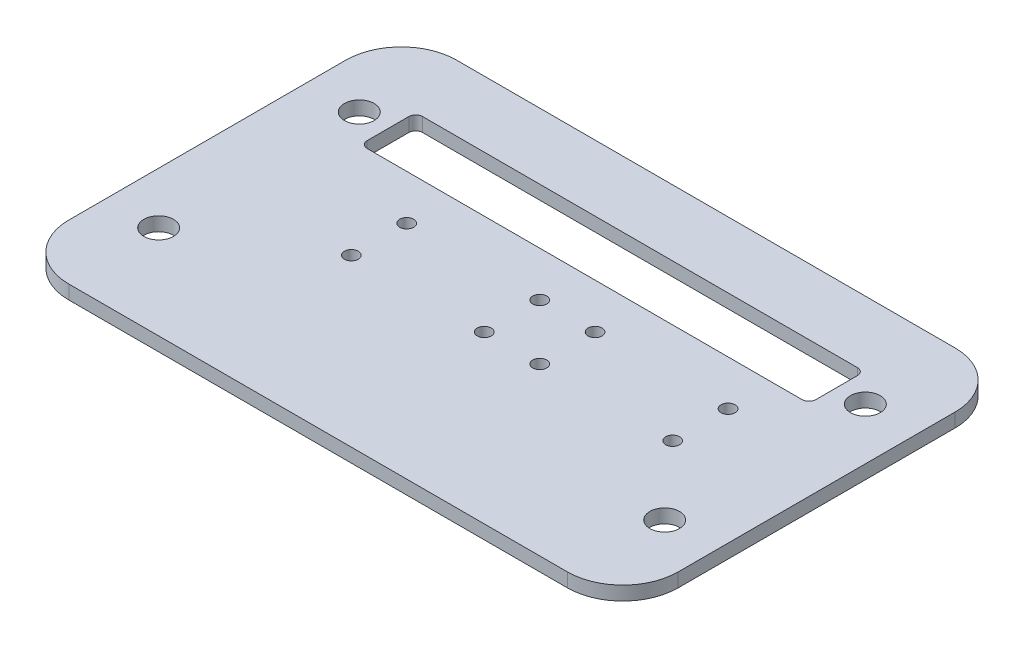
SolidWorks part; units mm, degrees
material "ABS"
ref_plane "Front Plane" through (0, 0, 0) normal (0, 0, 1) x (1, 0, 0)
ref_plane "Top Plane" through (0, 0, 0) normal (0, 1, 0) x (1, 0, 0)
ref_plane "Right Plane" through (0, 0, 0) normal (1, 0, 0) x (0, 0, -1)
sketch "Sketch2" plane through (0, 0, 0) normal (0, 1, 0) x (1, 0, 0)
  line L1 (-29, -11.5) -> (29, -11.5) construction
  line L2 (-29, -11.5) -> (-29, 11.5) construction
  line L3 (-29, 11.5) -> (29, 11.5) construction
  line L4 (29, -11.5) -> (29, 11.5) construction
  line L5 (-29, -11.5) -> (29, 11.5) construction
  line L6 (-29, 11.5) -> (29, -11.5) construction
  point P0 (0, 0)
  dimension "D1" = 58
  dimension "D2" = 23
sketch "Sketch3" plane through (0, 0, 0) normal (0, 1, 0) x (1, 0, 0)
  line L1 (-34.925, -22.225) -> (34.925, -22.225)
  line L2 (-34.925, -22.225) -> (-34.925, 22.225)
  line L3 (-34.925, 22.225) -> (34.925, 22.225)
  line L4 (34.925, -22.225) -> (34.925, 22.225)
  line L5 (-34.925, -22.225) -> (34.925, 22.225) construction
  line L6 (-34.925, 22.225) -> (34.925, -22.225) construction
  point P0 (0, 0)
  dimension "D1" = 44.45
  dimension "D2" = 69.85
extrude "Boss-Extrude1" add sketch "Sketch3" along normal blind 1.5875
hole_wizard "M3 Clearance Hole1" positions "Sketch4" profile "Sketch5" hole size "M3" standard "ANSI Metric" end condition through all
sketch "Sketch4" plane through (0, 1.5875, 0) normal (0, 1, 0) x (1, 0, 0)
  point P0 (-29, 11.5)
  point P3 (-29, -11.5)
  point P6 (29, -11.5)
  point P9 (29, 11.5)
sketch "Sketch5" plane through (-29, 1.5875, -11.5) normal (1, 0, 0) x (0, 0, 1)
  line L0 (0, 0) -> (0, 1.5875)
  line L1 (0, 1.5875) -> (1.7, 1.5875)
  line L2 (1.7, 1.5875) -> (1.7, 0)
  line L5 (1.7, 0) -> (0, 0)
  line L11 (0, -6.35) -> (0, 107.95) construction
  dimension "Thru Hole Dia." = 3.4
  dimension "Thru Hole Depth" = 1.5875
hole_wizard "Tap Drill for M2x0.4 Tap1" positions "Sketch6" profile "Sketch7" hole size "M2x0.4" standard "ANSI Metric" end condition through all
sketch "Sketch6" plane through (0, 1.5875, 0) normal (0, 1, 0) x (1, 0, 0)
  line L14 (0, 0) -> (34.925, 0) construction
  line L15 (34.925, -22.225) -> (34.925, 22.225) construction
  line L17 (-15.24, 3.175) -> (0, 3.175) construction
  line L20 (6.35, 3.175) -> (21.59, 3.175) construction
  line L23 (-15.24, -3.175) -> (0, -3.175) construction
  line L24 (0, 3.175) -> (0, -3.175) construction
  line L25 (6.35, -3.175) -> (21.59, -3.175) construction
  point P145 (-15.24, 3.175)
  point P148 (0, 3.175)
  point P151 (-15.24, -3.175)
  point P154 (0, -3.175)
  point P157 (6.35, 3.175)
  point P160 (21.59, 3.175)
  point P166 (0, 0)
  point P184 (6.35, -3.175)
  point P187 (21.59, -3.175)
  dimension "D1" = 15.24
  dimension "D2" = 6.35
  dimension "D3" = 6.35
  dimension "D4" = 6.35
sketch "Sketch7" plane through (21.59, 1.5875, 3.175) normal (1, 0, 0) x (0, 0, 1)
  line L0 (0, 0) -> (0, 1.5875)
  line L1 (0, 1.5875) -> (0.8, 1.5875)
  line L2 (0.8, 1.5875) -> (0.8, 0)
  line L5 (0.8, 0) -> (0, 0)
  line L11 (0, -6.35) -> (0, 107.95) construction
  dimension "Thru Hole Dia." = 1.6
  dimension "Thru Hole Depth" = 1.5875
fillet "Fillet1" radius 6.35 4 edges at (34.925, 0.7937, 22.225) (-34.925, 0.7937, -22.225) (34.925, 0.7937, -22.225) (-34.925, 0.7937, 22.225)
sketch "Sketch8" plane through (0, 1.5875, 0) normal (0, 1, 0) x (1, 0, 0)
  line L3 (-25.7125, 14.675) -> (25.7125, 14.675)
  line L7 (-25.7125, 14.675) -> (-25.7125, 8.325)
  line L8 (-25.7125, 8.325) -> (25.7125, 8.325)
  line L9 (25.7125, 14.675) -> (25.7125, 8.325)
  line L10 (-25.7125, 14.675) -> (25.7125, 8.325) construction
  line L11 (-25.7125, 8.325) -> (25.7125, 14.675) construction
  line L12 (-29, 11.5) -> (29, 11.5) construction
  circle A3 centre (-29, 11.5) radius 1.7 construction
  point P4 (0, 11.5)
  point P5 (0, 0)
  point P6 (0, 0)
  point P8 (-21.6182, 18.6745)
  point P10 (-25.4819, 8.9233)
  dimension "D2" = 6.35
  dimension "D1" = 1.5875
extrude "Cut-Extrude1" cut sketch "Sketch8" against normal through all
fillet "Fillet2" radius 0.7937 4 edges at (25.7125, 0.7937, -14.675) (25.7125, 0.7937, -8.325) (-25.7125, 0.7937, -8.325) (-25.7125, 0.7937, -14.675)
